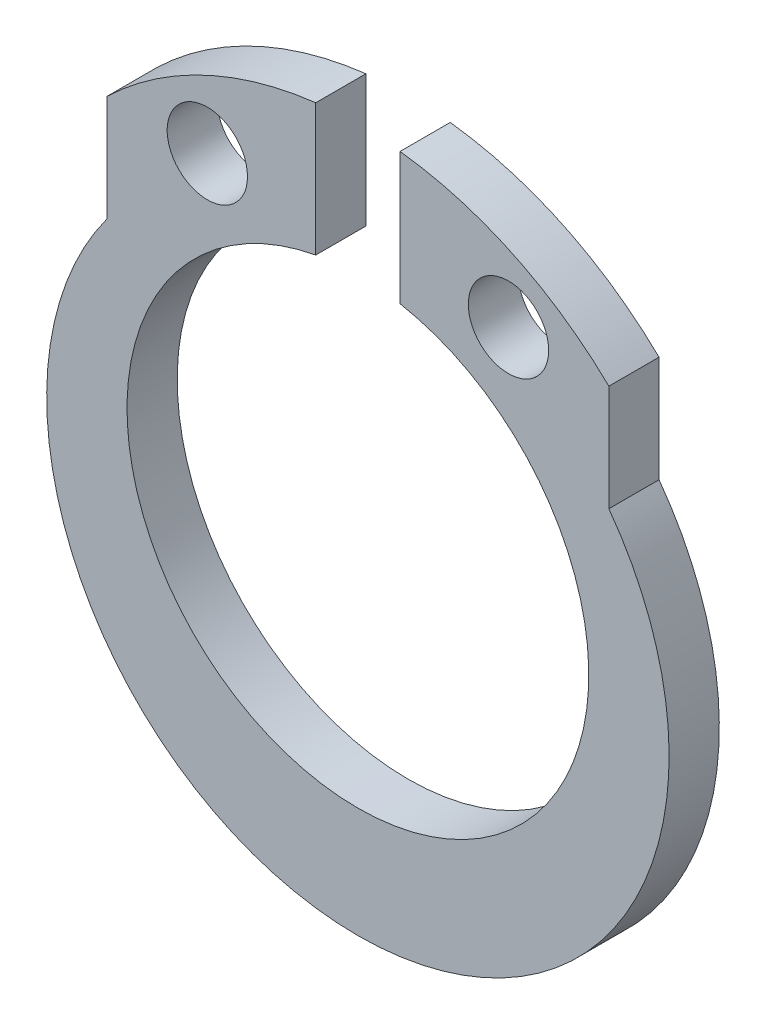
SolidWorks part; units mm, degrees
ref_plane "Front Plane" through (0, 0, 0) normal (0, 0, 1) x (1, 0, 0)
ref_plane "Top Plane" through (0, 0, 0) normal (0, 1, 0) x (1, 0, 0)
ref_plane "Right Plane" through (0, 0, 0) normal (1, 0, 0) x (0, 0, -1)
sketch "Sketch1" plane through (0, 0, 0) normal (0, 0, 1) x (1, 0, 0)
  line L0 (-2.5, 2.8904) -> (-2.5, 1.833)
  line L1 (0, 0) -> (0, 5.3312) construction
  line L2 (2.5, 2.8904) -> (2.5, 1.833)
  arc A0 (-2.5, 1.833) -> (2.5, 1.833) centre (0, 0) ccw
  arc A1 (2.5, 2.8904) -> (-2.5, 2.8904) centre (0, 0.3) ccw
  dimension "D1" = 6.2
  dimension "D2" = 0.3
  dimension "D4" = 3.6
  dimension "D3" = 5
extrude "Boss-Extrude1" add sketch "Sketch1" against normal blind 0.5 contours A1 L0 A0 L2
sketch "Sketch2" plane through (0, 0, 0) normal (0, 0, 1) x (1, 0, 0)
  circle A0 centre (0, 0.3) radius 2.3
  arc A1 (2.5, 2.8904) -> (-2.5, 2.8904) centre (0, 0.3) ccw construction
  dimension "D1" = 4.6
extrude "Cut-Extrude1" cut sketch "Sketch2" against normal through all
sketch "Sketch3" plane through (0, 0, 0) normal (0, 0, 1) x (1, 0, 0)
  line L0 (0, 0) -> (0, 3.9) construction
  line L3 (-0.42, 3.8754) -> (-0.42, 2.5613)
  line L5 (0.42, 3.8754) -> (0.42, 2.5613)
  arc A0 (2.5, 2.8904) -> (-2.5, 2.8904) centre (0, 0.3) ccw construction
  arc A1 (0.42, 3.8754) -> (-0.42, 3.8754) centre (0, 0.3) ccw
  circle A2 centre (0, 0.3) radius 2.3 construction
  arc A3 (0.42, 2.5613) -> (-0.42, 2.5613) centre (0, 0.3) ccw
  dimension "D1" = 0.84
extrude "Cut-Extrude2" cut sketch "Sketch3" against normal through all
hole_wizard "Ø0.8 (0.8) Diameter Hole1" positions "Sketch5" profile "Sketch4" hole size "Ø0.8" standard "DIN" end condition up to next
sketch "Sketch5" plane through (0, 0, 0) normal (0, 0, 1) x (1, 0, 0)
  line L0 (0, 0) -> (0, 4.3775) construction
  circle A0 centre (0, 0.3) radius 3 construction
  arc A1 (-0.42, 2.5613) -> (0.42, 2.5613) centre (0, 0.3) ccw construction
  point P6 (-1.5, 2.8981)
  point P8 (1.5, 2.8981)
  dimension "D1" = 6
  dimension "D2" = 3
sketch "Sketch4" plane through (-1.5, 2.8981, 0) normal (1, 0, 0) x (0, -1, 0)
  line L0 (0, 0) -> (0, 0.5)
  line L1 (0, 0.5) -> (0.4, 0.5)
  line L2 (0.4, 0.5) -> (0.4, 0)
  line L5 (0.4, 0) -> (0, 0)
  line L11 (0, -6.35) -> (0, 107.95) construction
  dimension "Thru Hole Dia." = 0.8
  dimension "Thru Hole Depth" = 0.5
